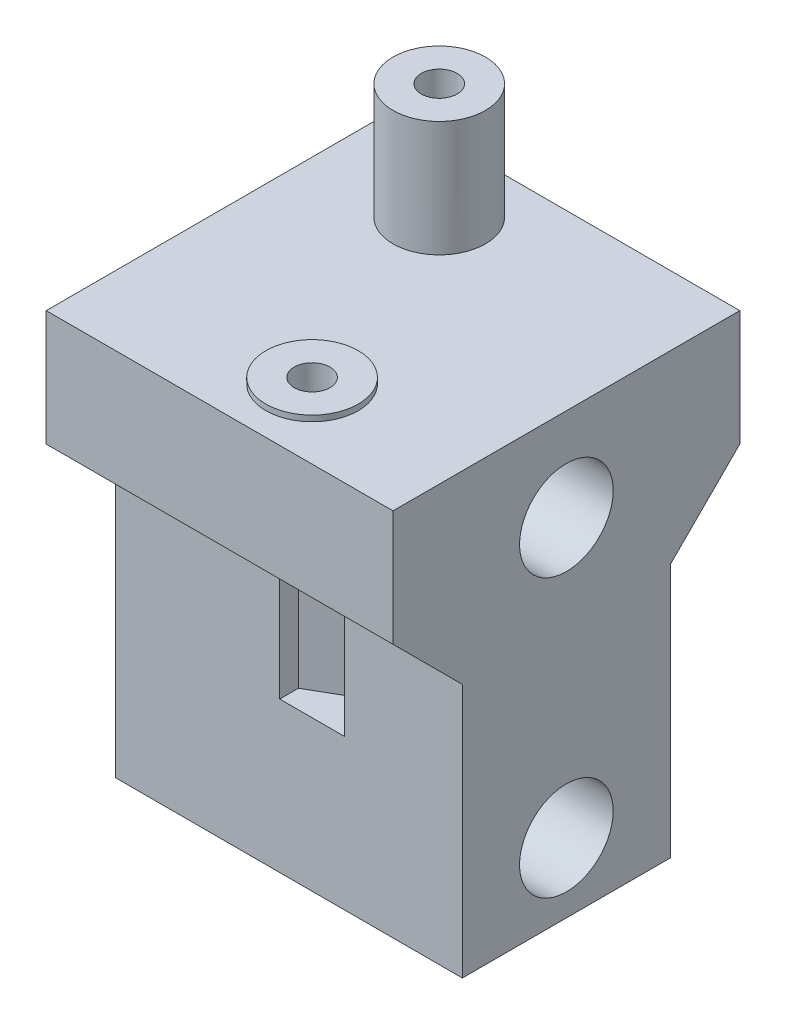
SolidWorks part; units mm, degrees
ref_plane "前视基准面" through (0, 0, 0) normal (0, 0, 1) x (1, 0, 0)
ref_plane "上视基准面" through (0, 0, 0) normal (0, 1, 0) x (1, 0, 0)
ref_plane "右视基准面" through (0, 0, 0) normal (1, 0, 0) x (0, 0, -1)
sketch "草图1" plane through (0, 0, 0) normal (0, 1, 0) x (1, 0, 0)
  line L0 (0, 0) -> (30, 0)
  line L1 (30, 0) -> (30, 30)
  line L2 (30, 30) -> (0, 30)
  line L3 (0, 30) -> (0, 0)
  dimension "D1" = 30
  dimension "D2" = 30
extrude "凸台-拉伸1" add sketch "草图1" along normal blind 38
sketch "草图3" plane through (0, 38, -50) normal (0, -1, 0) x (1, 0, 0)
  line L3 (30, 20) -> (0, 20) construction
  line L4 (30, 50) -> (30, 20) construction
  circle A0 centre (10, 26) radius 4
  dimension "D1" = 8
  dimension "D2" = 6
  dimension "D3" = 20
extrude "凸台-拉伸3" add sketch "草图3" against normal blind 10
sketch "草图7" plane through (0, 38, 0) normal (0, -1, 0) x (1, 0, 0)
  line L1 (30, 0) -> (30, -30) construction
  line L2 (0, 0) -> (30, 0) construction
  circle A0 centre (17, -6) radius 4
  dimension "D1" = 8
  dimension "D2" = 13
  dimension "D3" = 6
extrude "凸台-拉伸4" add sketch "草图7" against normal blind 0.5
ref_plane "基准面1" through (0, 28, 0) normal (0, 1, 0) x (1, 0, 0)
sketch "草图6" plane through (30, 0, 0) normal (1, 0, 0) x (0, 0, -1)
  line L0 (0, 38) -> (0, 0) construction
  line L1 (0, 0) -> (30, 0) construction
  circle A0 centre (15, 6) radius 4.05
  circle A1 centre (15, 30) radius 4.05
  dimension "D4" = 8.1
  dimension "D5" = 8.1
  dimension "D1" = 24
  dimension "D2" = 15
  dimension "D3" = 15
  dimension "D6" = 6
extrude "切除-拉伸3" cut sketch "草图6" against normal through all
sketch "草图9" plane through (0, 28, 0) normal (0, 1, 0) x (1, 0, 0)
  circle A0 centre (17, 6) radius 1.55
  circle A1 centre (10, 24) radius 1.55
  circle A2 centre (10, 24) radius 4 construction
  circle A3 centre (17, 6) radius 4 construction
  dimension "D1" = 3.1
  dimension "D2" = 3.1
extrude "切除-拉伸4" cut sketch "草图9" along normal through all
sketch "草图11" plane through (30, 0, 0) normal (1, 0, 0) x (0, 0, -1)
  line L0 (6, 0) -> (6, 22)
  line L1 (0, 0) -> (30, 0) construction
  line L2 (24, 0) -> (24, 22)
  line L3 (24, 22) -> (30, 28)
  line L4 (16.5, 28) -> (-16.5, 28) construction
  line L5 (30, 38) -> (30, 0) construction
  line L6 (30, 28) -> (30, 0)
  line L7 (30, 0) -> (24, 0)
  line L8 (6, 0) -> (0, 0)
  line L9 (0, 0) -> (0, 28)
  line L10 (0, 38) -> (0, 0) construction
  line L11 (0, 28) -> (6, 22)
  dimension "D1" = 45
  dimension "D2" = 45
  dimension "D3" = 6
  dimension "D4" = 6
extrude "切除-拉伸6" cut sketch "草图11" against normal through all
sketch "草图10" plane through (0, 28, 0) normal (0, 1, 0) x (1, 0, 0)
  line L0 (0, 0) -> (30, 0) construction
  line L1 (19.8, 0) -> (19.8, 7.6166)
  line L2 (19.8, 7.6166) -> (17, 9.2332)
  line L3 (17, 9.2332) -> (14.2, 7.6166)
  line L4 (14.2, 7.6166) -> (14.2, 0)
  line L7 (10, 20.7668) -> (12.8, 22.3834)
  line L8 (12.8, 22.3834) -> (12.8, 30)
  line L11 (7.2, 30) -> (7.2, 22.3834)
  line L12 (7.2, 22.3834) -> (10, 20.7668)
  line L14 (30, 0) -> (30, 30) construction
  line L15 (30, 30) -> (0, 30) construction
  line L16 (0, 30) -> (0, 0) construction
  line L17 (14.2, 4.3834) -> (17, 2.7668) [skipped]
  line L18 (17, 2.7668) -> (19.8, 4.3834) [skipped]
  line L19 (12.8, 25.6166) -> (10, 27.2332) [skipped]
  line L20 (10, 27.2332) -> (7.2, 25.6166) [skipped]
  line L21 (7.2, 30) -> (12.8, 30)
  line L22 (14.2, 0) -> (19.8, 0)
  circle A0 centre (17, 6) radius 2.8 construction
  circle A1 centre (10, 24) radius 2.8 construction
  circle A2 centre (10, 24) radius 1.55 construction
  circle A3 centre (17, 6) radius 1.55 construction
  dimension "D5" = 5.6
  dimension "D6" = 5.6
extrude "切除-拉伸5" cut sketch "草图10" against normal blind 15
sketch "草图12" plane through (0, 0, 0) normal (-1, 0, 0) x (0, 0, 1)
  line L0 (-24, 15) -> (-19.1, 15)
  line L1 (-24, 22) -> (-24, 0) construction
  line L9 (-19.1, 15) -> (-19.1, 0)
  line L10 (0, 28) -> (0, 38)
  line L11 (0, 38) -> (-30, 38)
  line L12 (-30, 38) -> (-30, 28)
  line L15 (-24, 0) -> (-6, 0)
  line L23 (-24, 0) -> (-19.1, 0)
  line L25 (-6, 0) -> (-6, 22)
  line L27 (-6, 22) -> (0, 28)
  line L28 (-30, 28) -> (-24, 22)
  line L29 (-24, 22) -> (-24, 0)
  line L30 (-24, 15) -> (-24, 0)
  dimension "D2" = 15
  dimension "D3" = 4.9
  dimension "D1" = 0
extrude "凸台-拉伸5" add sketch "草图12" along normal blind 7
sketch "草图14" plane through (-7, 0, 0) normal (-1, 0, 0) x (0, 0, 1)
  line L0 (-23.7, 15) -> (-23.7, 2)
  line L1 (-23.7, 2) -> (-24, 2)
  line L4 (-24, 0) -> (-19.1, 0)
  line L5 (-19.1, 0) -> (-19.1, 15)
  line L6 (-19.1, 15) -> (-24, 15)
  line L7 (-24, 15) -> (-24, 0)
  line L10 (-23.7, 15) -> (-24, 15)
  line L11 (-24, 15) -> (-24, 2)
  dimension "D2" = 0.3
  dimension "D3" = 13
  dimension "D1" = 0
extrude "切除-拉伸7" cut sketch "草图14" against normal blind 5
sketch "草图15" plane through (0, 0, -23.7) normal (0, 0, -1) x (-1, 0, 0)
  line L0 (2, 15) -> (7, 15) construction
  line L1 (7, 2) -> (7, 15) construction
  circle A0 centre (4, 12) radius 1
  circle A1 centre (4, 5.5) radius 1
  dimension "D1" = 2
  dimension "D2" = 2
  dimension "D3" = 3
  dimension "D4" = 6.5
  dimension "D5" = 3
  dimension "D6" = 3
extrude "切除-拉伸8" cut sketch "草图15" against normal through all
sketch "草图17" plane through (0, 0, -19.1) normal (0, 0, 1) x (1, 0, 0)
  line L1 (-1.95, 10.8164) -> (-1.95, 13.1836)
  line L2 (-1.95, 13.1836) -> (-4, 14.3671)
  line L3 (-4, 14.3671) -> (-6.05, 13.1836)
  line L4 (-6.05, 13.1836) -> (-6.05, 10.8164)
  line L5 (-6.05, 10.8164) -> (-4, 9.6329)
  line L6 (-4, 9.6329) -> (-1.95, 10.8164)
  line L7 (-7, 0) -> (-7, 15) construction
  line L8 (-1.95, 4.3164) -> (-1.95, 6.6836)
  line L9 (-1.95, 6.6836) -> (-4, 7.8671)
  line L10 (-4, 7.8671) -> (-6.05, 6.6836)
  line L11 (-6.05, 6.6836) -> (-6.05, 4.3164)
  line L12 (-6.05, 4.3164) -> (-4, 3.1329)
  line L13 (-4, 3.1329) -> (-1.95, 4.3164)
  circle A0 centre (-4, 12) radius 2.05 construction
  circle A1 centre (-4, 5.5) radius 2.05 construction
  dimension "D1" = 4.1
  dimension "D2" = 4.1
extrude "切除-拉伸10" cut sketch "草图17" against normal blind 1.8
